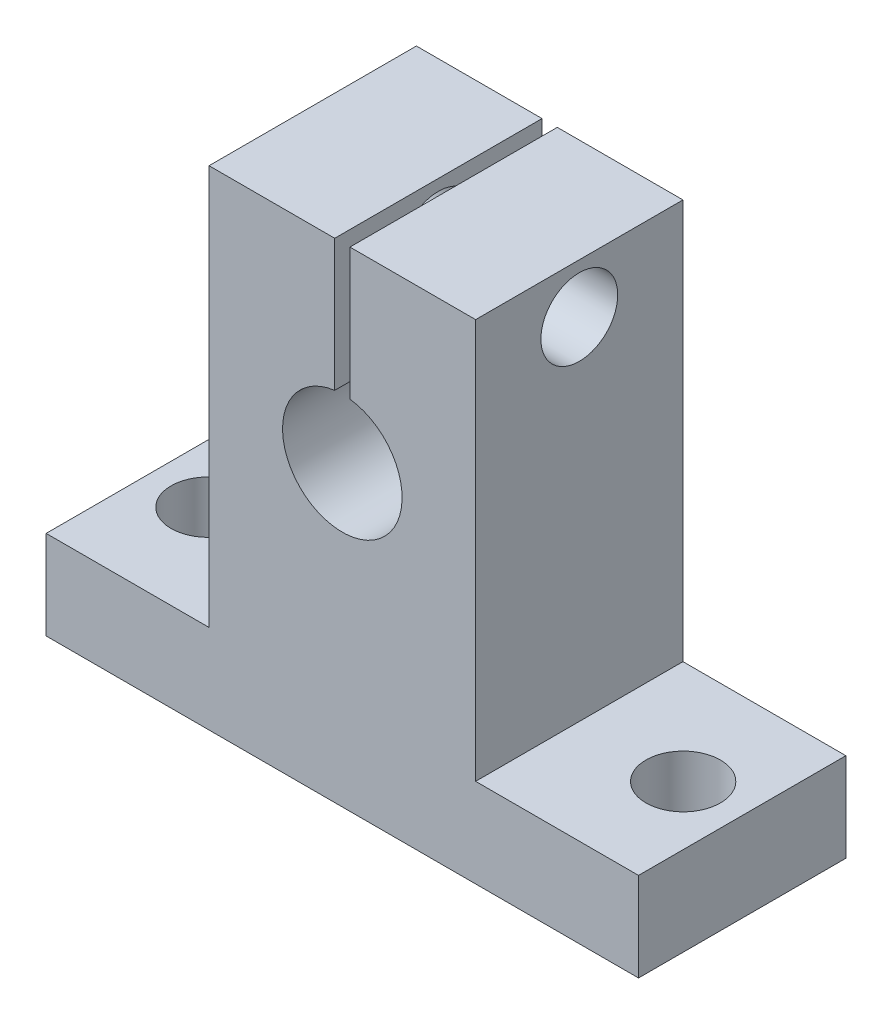
SolidWorks part; units mm, degrees
material "6061-T6 (SS)"
ref_plane "Alzado" through (0, 0, 0) normal (0, 0, 1) x (1, 0, 0)
ref_plane "Planta" through (0, 0, 0) normal (0, 1, 0) x (1, 0, 0)
ref_plane "Vista lateral" through (0, 0, 0) normal (1, 0, 0) x (0, 0, -1)
sketch "Croquis1" plane through (0, 0, 0) normal (0, 0, 1) x (1, 0, 0)
  line L1 (-2.0004, 17.6992) -> (15.9996, 17.6992)
  line L2 (-2.0004, 17.6992) -> (-2.0004, -9.3008)
  line L3 (-2.0004, -15.3008) -> (15.9996, -15.3008)
  line L4 (15.9996, 17.6992) -> (15.9996, -9.3008)
  line L5 (15.9996, -15.3008) -> (26.9996, -15.3008)
  line L7 (15.9996, -9.3008) -> (26.9996, -9.3008)
  line L8 (26.9996, -15.3008) -> (26.9996, -9.3008)
  line L9 (-2.0004, -15.3008) -> (-13.0004, -15.3008)
  line L11 (-2.0004, -9.3008) -> (-13.0004, -9.3008)
  line L12 (-13.0004, -15.3008) -> (-13.0004, -9.3008)
  dimension "D1" = 33
  dimension "D2" = 18
  dimension "D3" = 11
  dimension "D4" = 6
  dimension "D5" = 11
extrude "Saliente-Extruir1" add sketch "Croquis1" along normal blind 14 contours L9 L12 L11 L2 L1 L4 L7 L8 L5 L3
sketch "Croquis2" plane through (0, 0, 14) normal (0, 0, 1) x (1, 0, 0)
  line L0 (6.9996, -15.3008) -> (6.9996, 4.8031) construction
  line L1 (-13.0004, -15.3008) -> (26.9996, -15.3008) construction
  circle A0 centre (6.9996, 4.8031) radius 4.0356
extrude "Cortar-Extruir1" cut sketch "Croquis2" against normal blind 14
sketch "Croquis4" plane through (0, 0, 14) normal (0, 0, 1) x (1, 0, 0)
  line L0 (6.9996, -15.3008) -> (6.9996, 0.7674) construction
  line L1 (-13.0004, -15.3008) -> (26.9996, -15.3008) construction
  line L2 (6.9996, -11.9058) -> (-9.0658, -11.9058) construction
  line L3 (6.9996, -11.9058) -> (23.065, -11.9058) construction
  circle A0 centre (6.9996, 4.8031) radius 4.0356 construction
sketch "Croquis5" plane through (0, -9.3008, 0) normal (0, 1, 0) x (1, 0, 0)
  circle A0 centre (-9.0658, -7) radius 2.4977
sketch "Croquis7" plane through (0, -9.3008, 0) normal (0, 1, 0) x (1, 0, 0)
  line L0 (-9.0658, -7) -> (-13.0004, -7) construction
  line L1 (-13.0004, -14) -> (-13.0004, 0) construction
  line L2 (26.9996, -7) -> (23.0145, -7) construction
  line L3 (26.9996, -14) -> (26.9996, 0) construction
  circle A0 centre (23.0145, -7) radius 2.5149
extrude "Cortar-Extruir2" cut sketch "Croquis5" against normal blind 14 contours A0
extrude "Cortar-Extruir3" cut sketch "Croquis7" against normal blind 14 contours A0
sketch "Croquis8" plane through (0, 0, 14) normal (0, 0, 1) x (1, 0, 0)
  line L1 (6.4852, 18.6554) -> (7.5141, 18.6554)
  line L2 (6.4852, 18.6554) -> (6.4852, 8.216)
  line L3 (6.4852, 8.216) -> (7.5141, 8.216)
  line L4 (7.5141, 18.6554) -> (7.5141, 8.216)
  line L5 (6.4852, 18.6554) -> (7.5141, 8.216) construction
  line L6 (6.4852, 8.216) -> (7.5141, 18.6554) construction
  point P0 (6.9996, 13.4357)
extrude "Cortar-Extruir4" cut sketch "Croquis8" against normal blind 14
sketch "Croquis9" plane through (-2.0004, 0, 0) normal (-1, 0, 0) x (0, 0, 1)
  circle A0 centre (7, 14.3513) radius 2.594
extrude "Cortar-Extruir5" cut sketch "Croquis9" against normal through all contours A0
